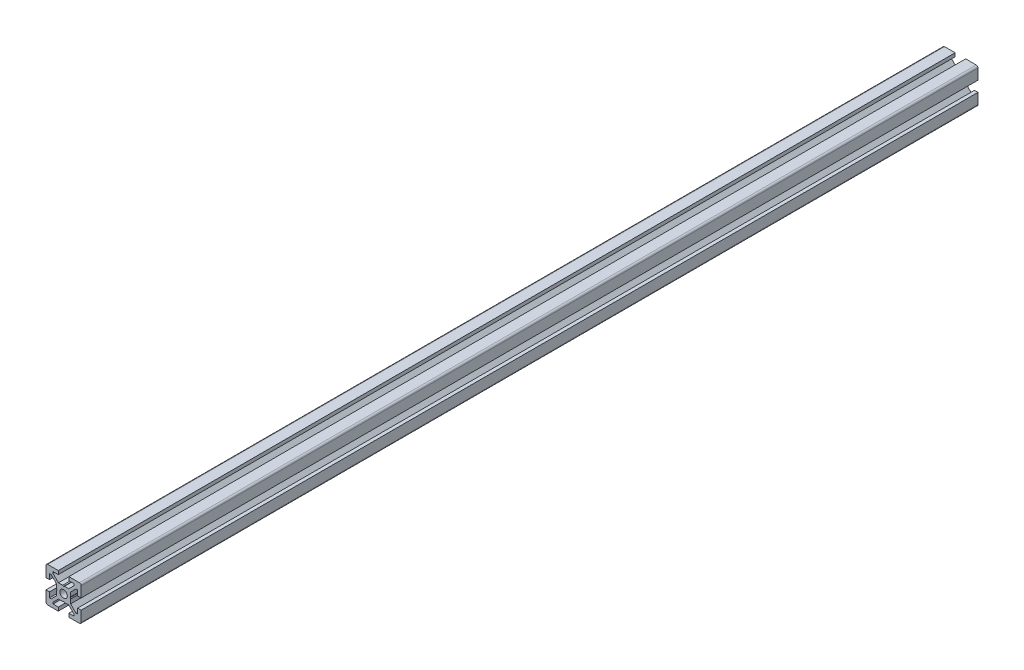
SolidWorks part; units mm, degrees
material "2014 合金"
ref_plane "正面" through (0, 0, 0) normal (0, 0, 1) x (1, 0, 0)
ref_plane "平面" through (0, 0, 0) normal (0, 1, 0) x (1, 0, 0)
ref_plane "右側面" through (0, 0, 0) normal (1, 0, 0) x (0, 0, -1)
ref_plane "平面1" through (0, 0, 0) normal (0, 0, 1) x (1, 0, 0)
sketch "ｽｹｯﾁ1" plane through (0, 0, 0) normal (0, 0, 1) x (1, 0, 0)
  line L0 (-10, -3) -> (-10, -9)
  line L1 (-9, -10) -> (-3, -10)
  line L2 (-3, -10) -> (-3, -8)
  line L3 (-3, -8) -> (-6, -8)
  line L4 (-6, -8) -> (-6, -7.0607)
  line L5 (-6, -7.0607) -> (-2.9393, -4)
  line L6 (-2.9393, -4) -> (-0.5196, -4)
  line L7 (-0.5196, -4) -> (0, -3.7)
  line L8 (0, -3.7) -> (0.5196, -4)
  line L9 (0.5196, -4) -> (2.9393, -4)
  line L10 (2.9393, -4) -> (6, -7.0607)
  line L11 (6, -7.0607) -> (6, -8)
  line L12 (6, -8) -> (3, -8)
  line L13 (3, -8) -> (3, -10)
  line L14 (3, -10) -> (9, -10)
  line L15 (10, -9) -> (10, -3)
  line L16 (10, -3) -> (8, -3)
  line L17 (8, -3) -> (8, -6)
  line L18 (8, -6) -> (7.0607, -6)
  line L19 (7.0607, -6) -> (4, -2.9393)
  line L20 (4, -2.9393) -> (4, -0.5196)
  line L21 (4, -0.5196) -> (3.7, 0)
  line L22 (3.7, 0) -> (4, 0.5196)
  line L23 (4, 0.5196) -> (4, 2.9393)
  line L24 (4, 2.9393) -> (7.0607, 6)
  line L25 (7.0607, 6) -> (8, 6)
  line L26 (8, 6) -> (8, 3)
  line L27 (8, 3) -> (10, 3)
  line L28 (10, 3) -> (10, 9)
  line L29 (9, 10) -> (3, 10)
  line L30 (3, 10) -> (3, 8)
  line L31 (3, 8) -> (6, 8)
  line L32 (6, 8) -> (6, 7.0607)
  line L33 (6, 7.0607) -> (2.9393, 4)
  line L34 (2.9393, 4) -> (0.5196, 4)
  line L35 (0.5196, 4) -> (0, 3.7)
  line L36 (0, 3.7) -> (-0.5196, 4)
  line L37 (-0.5196, 4) -> (-2.9393, 4)
  line L38 (-2.9393, 4) -> (-6, 7.0607)
  line L39 (-6, 7.0607) -> (-6, 8)
  line L40 (-6, 8) -> (-3, 8)
  line L41 (-3, 8) -> (-3, 10)
  line L42 (-3, 10) -> (-9, 10)
  line L43 (-10, 9) -> (-10, 3)
  line L44 (-10, 3) -> (-8, 3)
  line L45 (-8, 3) -> (-8, 6)
  line L46 (-8, 6) -> (-7.0607, 6)
  line L47 (-7.0607, 6) -> (-4, 2.9393)
  line L48 (-4, 2.9393) -> (-4, 0.5196)
  line L49 (-4, 0.5196) -> (-3.7, 0)
  line L50 (-3.7, 0) -> (-4, -0.5196)
  line L51 (-4, -0.5196) -> (-4, -2.9393)
  line L52 (-4, -2.9393) -> (-7.0607, -6)
  line L53 (-7.0607, -6) -> (-8, -6)
  line L54 (-8, -6) -> (-8, -3)
  line L55 (-8, -3) -> (-10, -3)
  arc A0 (-10, -9) -> (-9, -10) centre (-9, -9) ccw
  arc A1 (9, -10) -> (10, -9) centre (9, -9) ccw
  arc A2 (10, 9) -> (9, 10) centre (9, 9) ccw
  arc A3 (-9, 10) -> (-10, 9) centre (-9, 9) ccw
extrude "ﾎﾞｽ - 押し出し1" add sketch "ｽｹｯﾁ1" against normal blind 510
ref_plane "平面2" through (0, 0, 0) normal (1, 0, 0) x (0, 0, -1)
sketch "ｽｹｯﾁ2" plane through (0, 0, 0) normal (1, 0, 0) x (0, 0, -1)
  line L0 (0, 0) -> (0, 2.1)
  line L1 (0, 2.1) -> (260, 2.1)
  line L2 (260, 2.1) -> (260, 0)
  line L3 (260, 0) -> (0, 0)
  line L4 (260, 0) -> (0, 0) construction
revolve "ｶｯﾄ - 回転1" cut sketch "ｽｹｯﾁ2" angle 360 about L4
